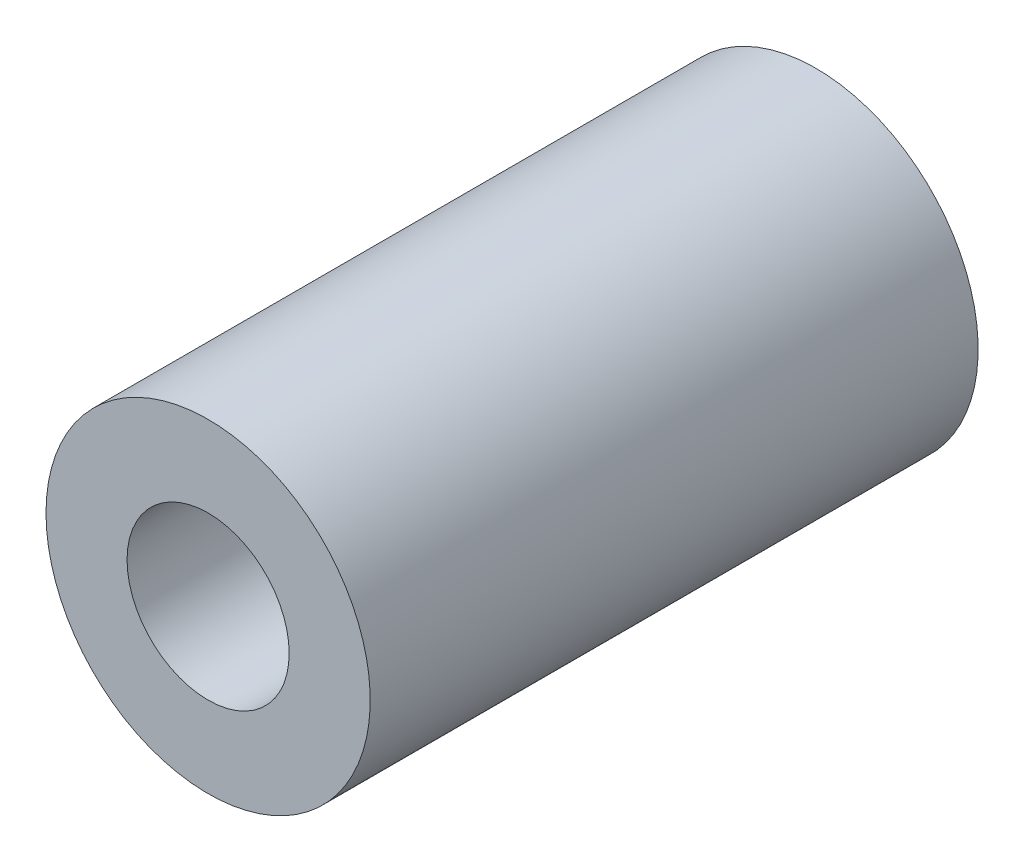
SolidWorks part; units mm, degrees
ref_plane "Front Plane" through (0, 0, 0) normal (0, 0, 1) x (1, 0, 0)
ref_plane "Top Plane" through (0, 0, 0) normal (0, 1, 0) x (1, 0, 0)
ref_plane "Right Plane" through (0, 0, 0) normal (1, 0, 0) x (0, 0, -1)
sketch "Sketch1" plane through (0, 0, 255.7071) normal (0, 0, -1) x (-1, 0, 0)
  circle A0 centre (-110.1646, 149.063) radius 2
  circle A1 centre (-110.1646, 149.063) radius 4
  dimension "D1" = 8
extrude "Boss-Extrude1" add sketch "Sketch1" along normal up to surface (15 mm away)
